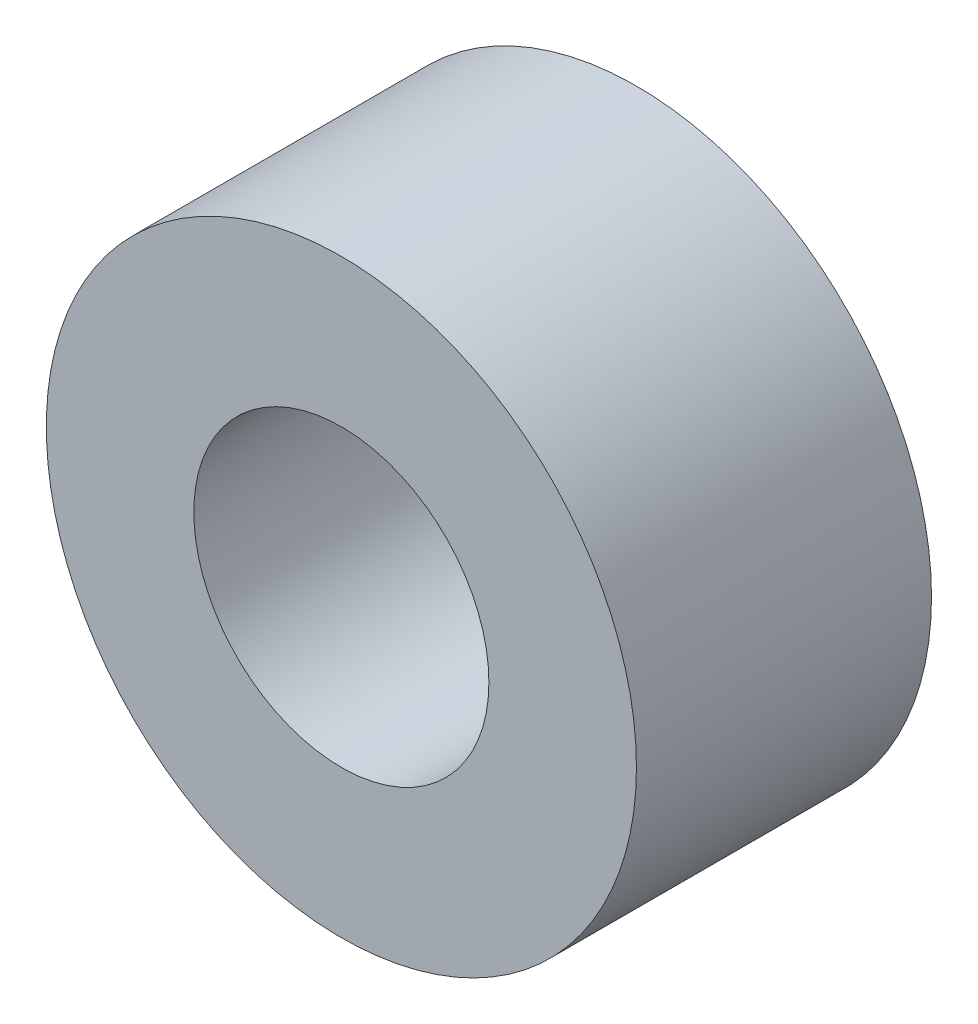
SolidWorks part; units mm, degrees
ref_plane "Front Plane" through (0, 0, 0) normal (0, 0, 1) x (1, 0, 0)
ref_plane "Top Plane" through (0, 0, 0) normal (0, 1, 0) x (1, 0, 0)
ref_plane "Right Plane" through (0, 0, 0) normal (1, 0, 0) x (0, 0, -1)
sketch "Sketch1" plane through (0, 0, 0) normal (0, 0, 1) x (1, 0, 0)
  circle A0 centre (0, 0) radius 6.35
  circle A1 centre (0, 0) radius 3.175
extrude "Boss-Extrude1" add sketch "Sketch1" along normal blind 6.35
